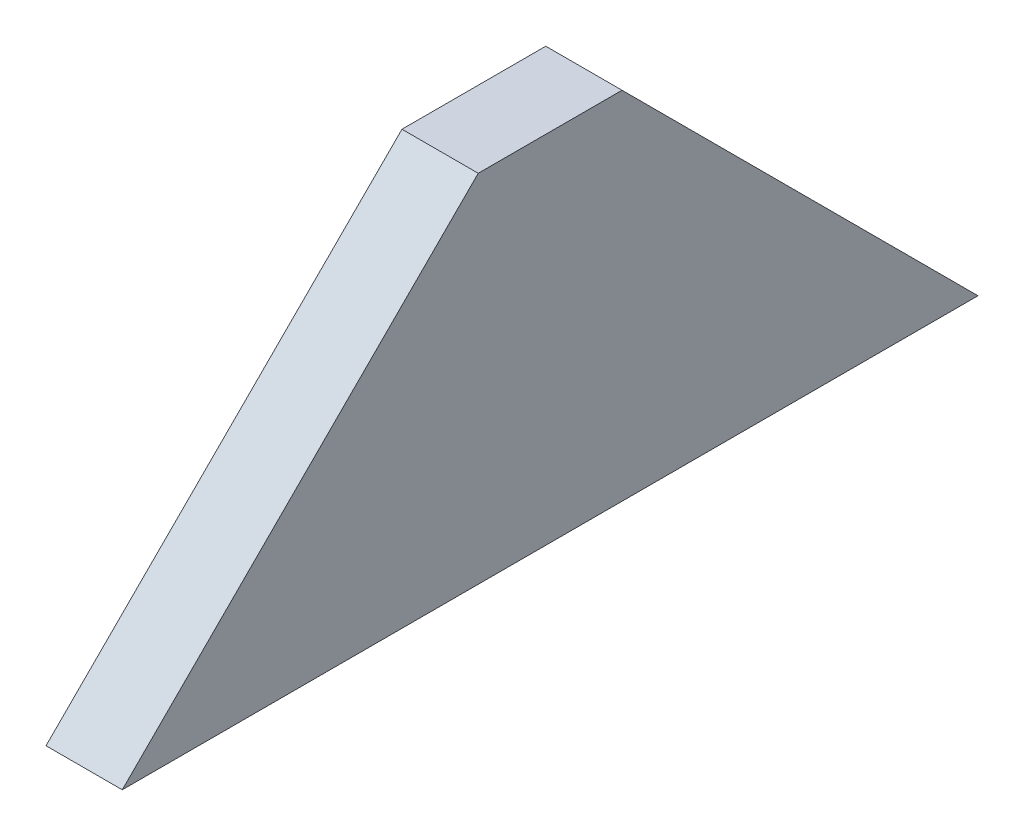
SolidWorks part; units mm, degrees
ref_plane "Front" through (0, 0, 0) normal (0, 0, 1) x (1, 0, 0)
ref_plane "Top" through (0, 0, 0) normal (0, 1, 0) x (1, 0, 0)
ref_plane "Right" through (0, 0, 0) normal (1, 0, 0) x (0, 0, -1)
sketch "Sketch1" plane through (0, 0, 0) normal (1, 0, 0) x (0, 0, -1)
  line L0 (92.2993, 18.4305) -> (92.2993, -70.4695) construction
  line L1 (74.3415, 18.4305) -> (110.2571, 18.4305)
  line L2 (74.3415, 18.4305) -> (-14.5585, -70.4695)
  line L3 (-14.5585, -70.4695) -> (199.1571, -70.4695)
  line L4 (110.2571, 18.4305) -> (199.1571, -70.4695)
extrude "Extrude1" add sketch "Sketch1" against normal blind 19.05
